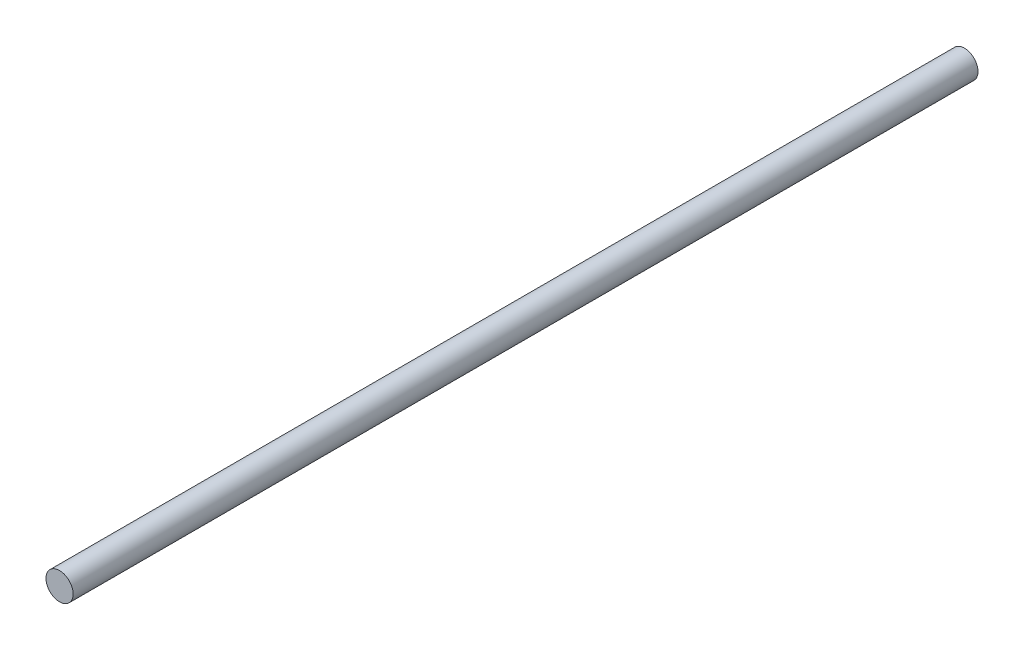
SolidWorks part; units mm, degrees
ref_plane "Front Plane" through (0, 0, 0) normal (0, 0, 1) x (1, 0, 0)
ref_plane "Top Plane" through (0, 0, 0) normal (0, 1, 0) x (1, 0, 0)
ref_plane "Right Plane" through (0, 0, 0) normal (1, 0, 0) x (0, 0, -1)
sketch "Sketch1" plane through (0, 0, 0) normal (0, 0, 1) x (1, 0, 0)
  circle A0 centre (0, 0) radius 3
extrude "Boss-Extrude1" add sketch "Sketch1" along normal blind 200
